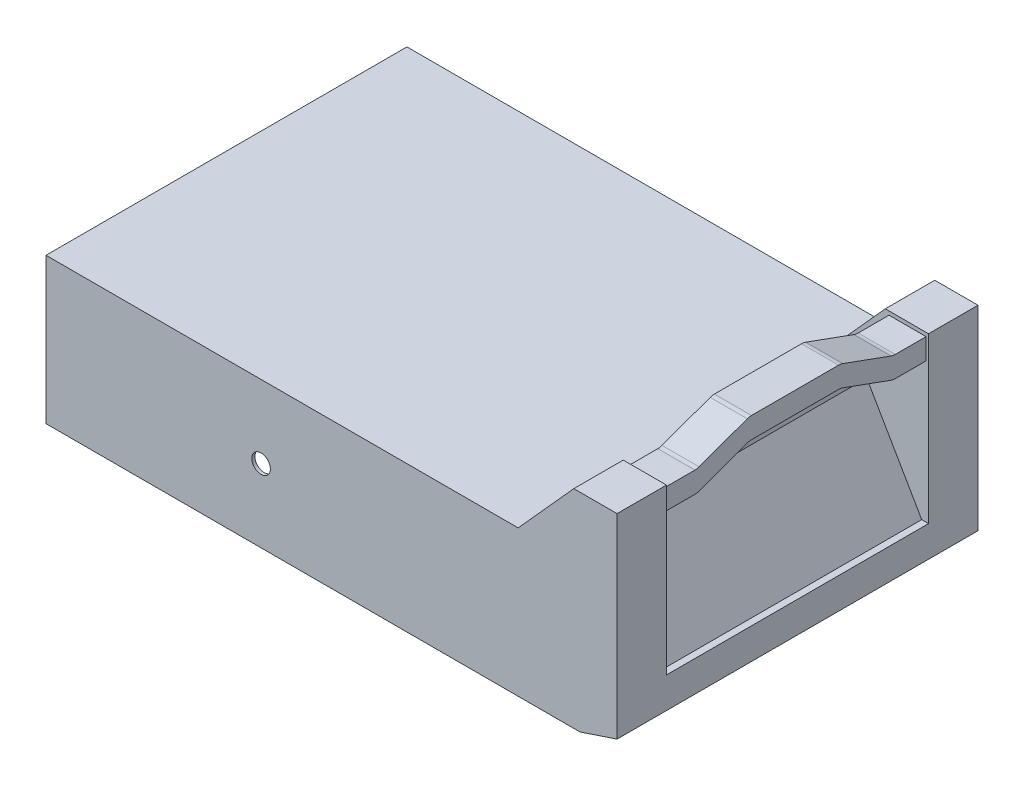
SolidWorks part; units mm, degrees
material "ABS"
ref_plane "Front Plane" through (0, 0, 0) normal (0, 0, 1) x (1, 0, 0)
ref_plane "Top Plane" through (0, 0, 0) normal (0, 1, 0) x (1, 0, 0)
ref_plane "Right Plane" through (0, 0, 0) normal (1, 0, 0) x (0, 0, -1)
sketch "Sketch1" plane through (0, 0, 0) normal (0, 1, 0) x (1, 0, 0)
  line L0 (201, 146) -> (201, -146) construction
  line L1 (231, -146) -> (-231, -146)
  line L2 (231, -146) -> (231, 146)
  line L3 (231, 146) -> (-231, 146)
  line L4 (-231, -146) -> (-231, 146)
  line L5 (231, -146) -> (-231, 146) construction
  line L6 (231, 146) -> (-231, -146) construction
  point P0 (0, 0)
  dimension "D1" = 462
  dimension "D2" = 292
  dimension "D3" = 432
extrude "Boss-Extrude1" add sketch "Sketch1" along normal blind 118
chamfer "Chamfer1" distance 30 distance2 10 1 edges at (231, 0, 0)
sketch "Sketch2" plane through (0, 118, 0) normal (0, 1, 0) x (1, 0, 0)
  line L0 (0, 0) -> (339.2348, 0) construction
  line L1 (231, 146) -> (151, 146)
  line L2 (231, 146) -> (231, 106)
  line L3 (231, 106) -> (151, 106)
  line L4 (151, 146) -> (151, 106)
  line L5 (231, -106) -> (151, -106)
  line L6 (151, -146) -> (151, -106)
  line M5 (-231, -146) -> (231, -146)
  line M6 (231, -146) -> (231, 146)
  line M7 (231, 146) -> (-231, 146)
  dimension "D1" = 80
  dimension "D2" = 40
extrude "Boss-Extrude2" add sketch "Sketch2" along normal blind 50 contours L4 L3 M7 M6 | L6 L5 M5 M6
sketch "Sketch3" plane through (0, 0, 146) normal (0, 0, 1) x (1, 0, 0)
  line L0 (151, 118) -> (196, 168)
  line L1 (151, 168) -> (231, 168) construction
  line L2 (196, 168) -> (151, 168)
  line L3 (151, 168) -> (151, 118)
  dimension "D1" = 45
extrude "Cut-Extrude1" cut sketch "Sketch3" against normal through all
sketch "Sketch5" plane through (231, 0, 0) normal (1, 0, 0) x (0, 0, -1)
  line L0 (106, 168) -> (106, 118) construction
  line L1 (-106, 118) -> (106, 118)
  line L2 (-106, 118) -> (-106, 35)
  line L3 (-106, 35) -> (106, 35)
  line L4 (106, 118) -> (106, 35)
  line L6 (146, 0) -> (-146, 0) construction
  dimension "D1" = 35
extrude "Cut-Extrude3" cut sketch "Sketch5" against normal blind 50
ref_plane "Plane2" through (199, 0, 0) normal (1, 0, 0) x (0, 0, -1)
sketch "Sketch6" plane through (199, 0, 0) normal (1, 0, 0) x (0, 0, -1)
  line L0 (106, 165) -> (81.0494, 165)
  line L1 (106, 118) -> (106, 168) construction
  line L2 (77.6292, 165.6031) -> (38.6569, 179.7878)
  line L3 (35.2367, 180.3909) -> (-35.2367, 180.3909)
  line L4 (0, 118) -> (0, 226.6018) construction
  line L5 (146, 118) -> (-146, 118) construction
  line L6 (106, 148) -> (81.0494, 148)
  line L7 (77.6292, 148.6031) -> (38.6569, 162.7878)
  line L8 (35.2367, 163.3909) -> (-35.2367, 163.3909)
  line L9 (-77.6292, 148.6031) -> (-38.6569, 162.7878)
  line L10 (-77.6292, 165.6031) -> (-38.6569, 179.7878)
  line L11 (-106, 148) -> (-81.0494, 148)
  line L12 (-106, 165) -> (-81.0494, 165)
  line L13 (106, 165) -> (106, 148)
  line L14 (-106, 165) -> (-106, 148)
  arc A0 (81.0494, 148) -> (77.6292, 148.6031) centre (81.0494, 158) cw
  arc A1 (38.6569, 162.7878) -> (35.2367, 163.3909) centre (35.2367, 153.3909) ccw
  arc A2 (35.2367, 180.3909) -> (38.6569, 179.7878) centre (35.2367, 170.3909) cw
  arc A3 (77.6292, 165.6031) -> (81.0494, 165) centre (81.0494, 175) ccw
  arc A4 (-38.6569, 162.7878) -> (-35.2367, 163.3909) centre (-35.2367, 153.3909) cw
  arc A5 (-35.2367, 180.3909) -> (-38.6569, 179.7878) centre (-35.2367, 170.3909) ccw
  arc A6 (-77.6292, 165.6031) -> (-81.0494, 165) centre (-81.0494, 175) cw
  arc A7 (-81.0494, 148) -> (-77.6292, 148.6031) centre (-81.0494, 158) ccw
  point P24 (79.2862, 148)
  point P27 (37, 163.3909)
  point P30 (37, 180.3909)
  point P33 (79.2862, 165)
  point P35 (0, 180.3909)
  point P36 (0, 163.3909)
  dimension "D9" = 10
  dimension "D1" = 160
  dimension "D2" = 45
  dimension "D3" = 47
  dimension "D4" = 37
  dimension "D5" = 37
  dimension "D6" = 45
  dimension "D7" = 160
  dimension "D8" = 30
extrude "Boss-Extrude3" add sketch "Sketch6" along normal blind 30
sketch "Sketch8" plane through (0, 0, -106) normal (0, 0, 1) x (1, 0, 0)
  line L0 (231, 140.8675) -> (181, 112) construction
  line L1 (231, 168) -> (231, 35) construction
  line L2 (181, 35) -> (181, 118) construction
  line L3 (181, 35) -> (231, 35) construction
  line L4 (181, 112) -> (256.685, -19.0903) construction
  line L5 (181, 112) -> (225.456, 35)
  line L6 (225.456, 35) -> (181, 35)
  line L7 (181, 35) -> (181, 112)
  dimension "D1" = 30
  dimension "D2" = 6
extrude "Boss-Extrude5" add sketch "Sketch8" along normal up to next
shell "Shell1" thickness 2.5
sketch "Sketch9" plane through (0, 0, 146) normal (0, 0, 1) x (1, 0, 0)
  line L0 (-231, 118) -> (-231, 0) construction
  line L1 (-231, 0) -> (201, 0) construction
  circle A0 centre (-57, 59) radius 7.5
  dimension "D2" = 15
  dimension "D1" = 174
  dimension "D3" = 59
extrude "Cut-Extrude4" cut sketch "Sketch9" against normal through all
